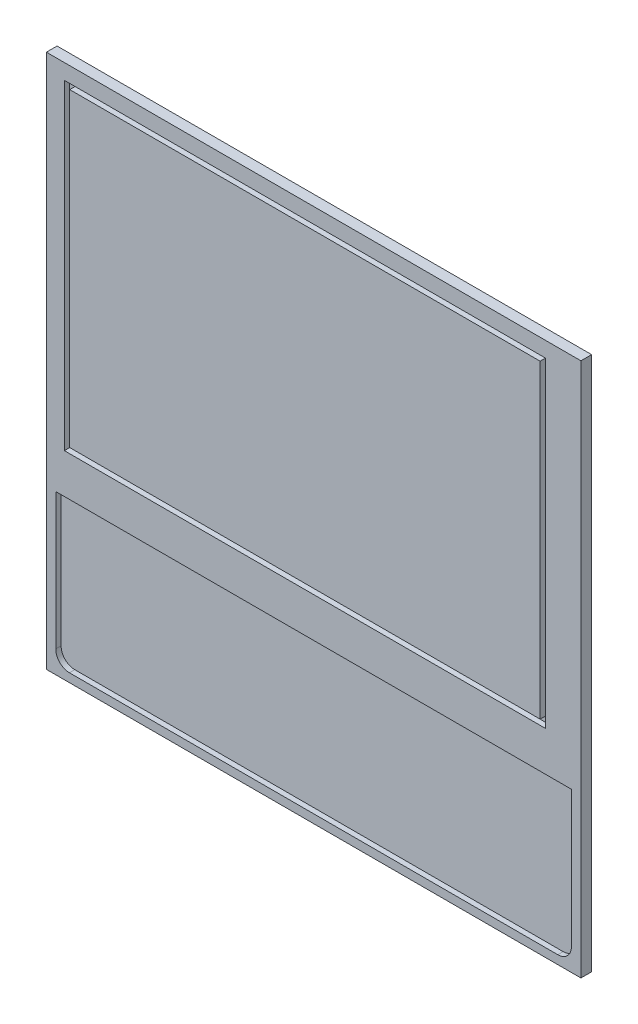
SolidWorks part; units mm, degrees
ref_plane "Front Plane" through (0, 0, 0) normal (0, 0, 1) x (1, 0, 0)
ref_plane "Top Plane" through (0, 0, 0) normal (0, 1, 0) x (1, 0, 0)
ref_plane "Right Plane" through (0, 0, 0) normal (1, 0, 0) x (0, 0, -1)
sketch "Sketch2" plane through (0, 0, 0) normal (0, 0, 1) x (1, 0, 0)
  line L1 (-250, 250) -> (250, 250)
  line L2 (-250, 250) -> (-250, -250)
  line L3 (-250, -250) -> (250, -250)
  line L4 (250, 250) -> (250, -250)
  line L5 (-250, 250) -> (250, -250) construction
  line L6 (-250, -250) -> (250, 250) construction
  point P0 (0, 0)
  dimension "D1" = 500
  dimension "D2" = 500
extrude "Boss-Extrude1" add sketch "Sketch2" along normal blind 10
sketch "Sketch4" plane through (0, 0, 10) normal (0, 0, 1) x (1, 0, 0)
  line L0 (241.0651, -229.241) -> (241.2197, -101.5338)
  line L1 (-241.1704, -101.5338) -> (241.2197, -101.5338)
  line L2 (-241.1704, -101.5338) -> (-241.1704, -228.9463)
  line L3 (-228.4613, -241.9535) -> (228.3526, -241.9535)
  line L5 (-241.1704, -101.5338) -> (241.2197, -241.9535) construction
  line L6 (-244.9309, -241.9535) -> (241.2197, -101.5338) construction
  arc A0 (-241.1704, -228.9463) -> (-228.4613, -241.9535) centre (-228.4613, -229.241) ccw
  arc A1 (228.3526, -241.9535) -> (241.0651, -229.241) centre (228.3526, -229.241) ccw
  point P0 (-0.9118, -171.4711)
extrude "Cut-Extrude1" cut sketch "Sketch4" against normal blind 5
sketch "Sketch5" plane through (0, 0, 10) normal (0, 0, 1) x (1, 0, 0)
  line L1 (-233.1598, 235.6039) -> (216.8402, 235.6039)
  line L2 (-233.1598, 235.6039) -> (-233.1598, -64.3961)
  line L3 (-233.1598, -64.3961) -> (216.8402, -64.3961)
  line L4 (216.8402, 235.6039) -> (216.8402, -64.3961)
  line L7 (-228.1598, 230.6039) -> (211.8402, 230.6039)
  line L8 (-228.1598, 230.6039) -> (-228.1598, -59.3961)
  line L9 (-228.1598, -59.3961) -> (211.8402, -59.3961)
  line L10 (211.8402, 230.6039) -> (211.8402, -59.3961)
  point P0 (0, 80.2987)
  point P5 (0, 80.2987)
  dimension "D1" = 450
  dimension "D2" = 300
  dimension "D3" = 5
  dimension "D4" = 440
  dimension "D5" = 5
  dimension "D6" = 5
  dimension "D7" = 5
extrude "Cut-Extrude2" cut sketch "Sketch5" against normal blind 5
